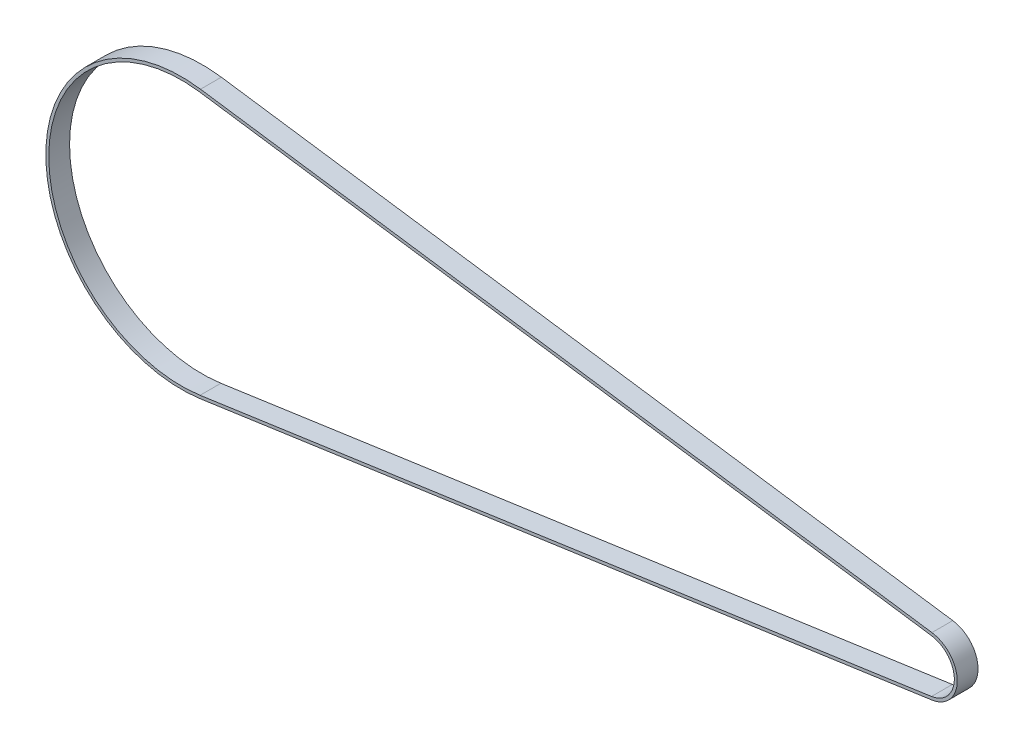
SolidWorks part; units mm, degrees
ref_plane "Front Plane" through (0, 0, 0) normal (0, 0, 1) x (1, 0, 0)
ref_plane "Top Plane" through (0, 0, 0) normal (0, 1, 0) x (1, 0, 0)
ref_plane "Right Plane" through (0, 0, 0) normal (1, 0, 0) x (0, 0, -1)
sketch "Sketch2" plane through (0, 0, 0) normal (0, 0, 1) x (1, 0, 0)
  line L0 (0, 0) -> (1, 0) construction
  line L1 (0, 0) -> (0, 1) construction
  line L2 (2.5778, -17.9771) -> (-497.1471, -89.6342)
  line L3 (-497.1471, 89.6342) -> (2.5778, 17.9771)
  arc A0 (2.5778, 17.9771) -> (2.5778, -17.9771) centre (0, 0) cw
  arc A1 (-497.1471, -89.6342) -> (-497.1471, 89.6342) centre (-510, 0) cw
extrude "Extrude-Thin1" add sketch "Sketch2" along normal blind 14.224 thin thin type one direction wall 2
